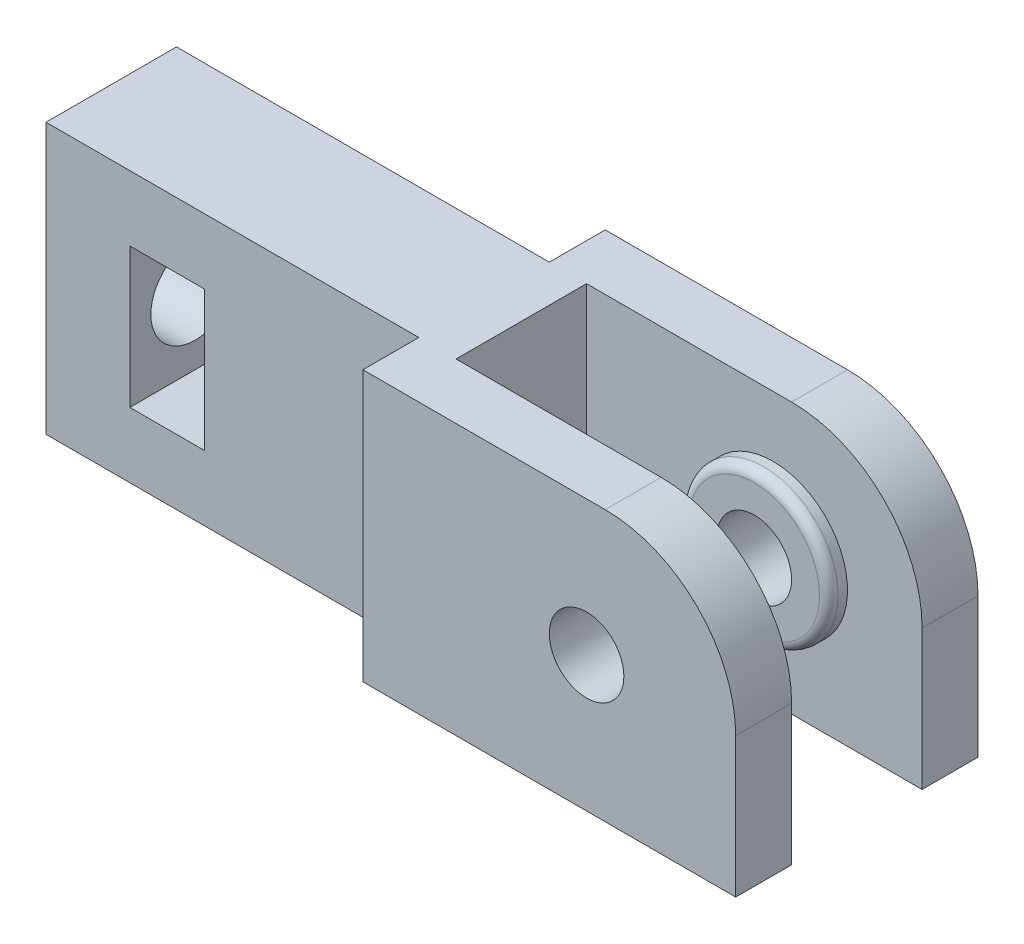
SolidWorks part; units mm, degrees
ref_plane "Plan de face" through (0, 0, 0) normal (0, 0, 1) x (1, 0, 0)
ref_plane "Plan de dessus" through (0, 0, 0) normal (0, 1, 0) x (1, 0, 0)
ref_plane "Plan de droite" through (0, 0, 0) normal (1, 0, 0) x (0, 0, -1)
sketch "Esquisse2" plane through (0, 0, 0) normal (0, 1, 0) x (1, 0, 0)
  line L0 (0, 0) -> (0, 3.5)
  line L1 (0, 3.5) -> (20, 3.5)
  line L2 (20, 3.5) -> (20, 6.5)
  line L3 (20, 6.5) -> (40, 6.5)
  line L4 (40, 6.5) -> (40, 3.5)
  line L5 (40, 3.5) -> (22, 3.5)
  line L6 (22, 3.5) -> (22, 0)
  line L7 (22, 0) -> (0, 0)
  dimension "D1" = 20
  dimension "D2" = 3
  dimension "D3" = 3
  dimension "D4" = 3.5
  dimension "D5" = 18
extrude "Boss.-Extru.1" add sketch "Esquisse2" along normal blind 14.5
fillet "Congé5" radius 7 1 edges at (40, 14.5, -5)
sketch "Esquisse3" plane through (0, 0, -3.5) normal (0, 0, 1) x (1, 0, 0)
  line L0 (40, 7.25) -> (32, 7.25) construction
  line L1 (32, 14.5) -> (32, 0) construction
  line L2 (22, 14.5) -> (33, 14.5) construction
  line L3 (22, 0) -> (40, 0) construction
  line L4 (40, 7.5) -> (40, 0) construction
  circle A0 centre (32, 7.25) radius 4
  dimension "D1" = 8
  dimension "D2" = 8
extrude "Boss.-Extru.2" add sketch "Esquisse3" along normal blind 1
fillet "Congé2" radius 0.5 1 edges at (36, 7.25, -2.5)
sketch "Esquisse4" plane through (0, 0, -2.5) normal (0, 0, 1) x (1, 0, 0)
  circle A0 centre (32, 7.25) radius 2
  dimension "D1" = 4
extrude "Enlèv. mat.-Extru.1" cut sketch "Esquisse4" against normal through all
mirror "Symétrie1" about plane through (22, 14.5, 0) normal (0, 0, -1) of bodies 103
sketch "Esquisse5" plane through (0, 0, 0) normal (-1, 0, 0) x (0, 0, 1)
  line L0 (0, 7.25) -> (3.5, 7.25) construction
  line L1 (3.5, 14.5) -> (3.5, 0) construction
  line L2 (0, 7.25) -> (0, 0) construction
  circle A0 centre (0, 7.25) radius 2.375
  dimension "D1" = 4.75
extrude "Enlèv. mat.-Extru.2" cut sketch "Esquisse5" against normal through all
sketch "Esquisse6" plane through (0, 0, -3.5) normal (0, 0, -1) x (-1, 0, 0)
  line L0 (-6.5, 7.25) -> (0, 7.25) construction
  line L1 (-8.5, 11) -> (-4.5, 11)
  line L2 (-8.5, 11) -> (-8.5, 3.5)
  line L3 (-8.5, 3.5) -> (-4.5, 3.5)
  line L4 (-4.5, 11) -> (-4.5, 3.5)
  line L5 (-8.5, 11) -> (-4.5, 3.5) construction
  line L6 (-8.5, 3.5) -> (-4.5, 11) construction
  line L7 (0, 14.5) -> (0, 0) construction
  point P0 (-6.5, 7.25)
  dimension "D1" = 7.5
  dimension "D2" = 4
  dimension "D3" = 6.5
extrude "Enlèv. mat.-Extru.3" cut sketch "Esquisse6" against normal through all
